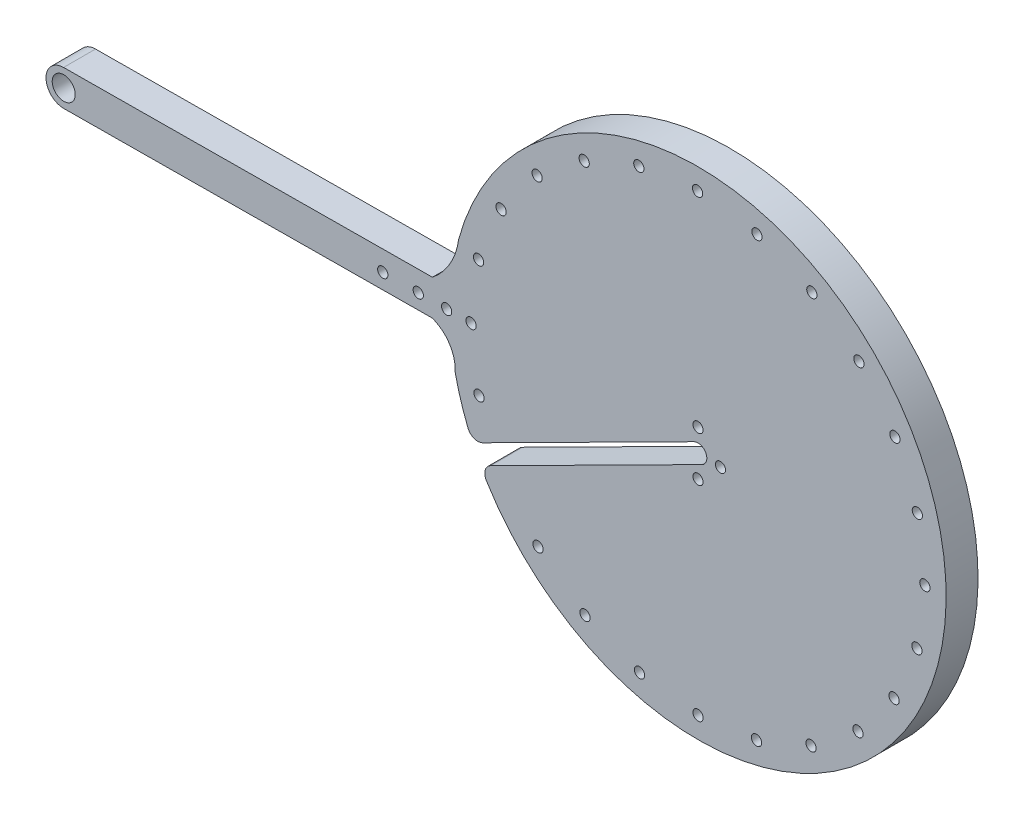
SolidWorks part; units mm, degrees
ref_plane "Front Plane" through (0, 0, 0) normal (0, 0, 1) x (1, 0, 0)
ref_plane "Top Plane" through (0, 0, 0) normal (0, 1, 0) x (1, 0, 0)
ref_plane "Right Plane" through (0, 0, 0) normal (1, 0, 0) x (0, 0, -1)
sketch "Sketch1" plane through (0, 0, 0) normal (0, 0, 1) x (1, 0, 0)
  line L0 (-134.2203, 11.2119) -> (-30.2577, 11.9893)
  line L1 (-30.2577, 21.9896) -> (-30.2577, 11.9893) construction
  line L2 (43.5222, 18.6947) -> (-18.9371, -12.8108)
  line L3 (45.774, 14.2305) -> (-16.6852, -17.275)
  line L5 (-30.2577, 21.9896) -> (-134.2951, 21.2116)
  arc A0 (-23.8494, 2.0369) -> (-30.2577, 11.9893) centre (-33.8306, 2.6493) ccw
  circle A1 centre (44.6612, 22.8126) radius 1.4225
  circle A2 centre (-17.1051, -0.3465) radius 1.45
  arc A3 (-30.2577, 21.9896) -> (-22.8366, 35.0587) centre (-42.6646, 37.6762) ccw
  arc A4 (-134.2951, 21.2116) -> (-134.2203, 11.2119) centre (-134.2577, 16.2117) ccw
  circle A5 centre (-134.2577, 16.2117) radius 3.25
  circle A6 centre (-17.2348, 32.7878) radius 1.45
  circle A7 centre (-10.8866, 48.273) radius 1.45
  circle A8 centre (-19.3514, 16.2033) radius 1.45
  circle A9 centre (-44.2577, 16.208) radius 1.45
  circle A10 centre (-34.2577, 16.2117) radius 1.45
  circle A11 centre (-26.2577, 16.2117) radius 1.45
  circle A12 centre (50.9928, 16.204) radius 1.4225
  circle A13 centre (44.6602, 10.1126) radius 1.4225
  circle A14 centre (106.403, -0.3402) radius 1.45
  circle A15 centre (99.9645, -15.7258) radius 1.45
  circle A16 centre (89.7798, -28.915) radius 1.45
  circle A17 centre (76.5456, -39.0221) radius 1.45
  circle A18 centre (61.1596, -45.3708) radius 1.45
  circle A19 centre (44.6606, -47.5374) radius 1.45
  circle A20 centre (28.16, -45.3771) radius 1.45
  circle A21 centre (12.7695, -39.0329) radius 1.45
  circle A22 centre (-0.471, -28.9276) radius 1.45
  arc A23 (114.5859, 13.512) -> (-22.8366, 35.0587) centre (44.6481, 16.4626) ccw
  arc A24 (-23.8494, 2.0369) -> (-18.9371, -12.8108) centre (44.6481, 16.4626) ccw
  arc A25 (-16.6852, -17.275) -> (114.5859, 13.512) centre (44.6481, 16.4626) ccw
  arc A33 (45.774, 14.2305) -> (43.5222, 18.6947) centre (44.6481, 16.4626) ccw
  circle A34 centre (-0.7303, 61.5936) radius 1.45
  circle A35 centre (12.545, 71.8285) radius 1.45
  circle A36 centre (27.9686, 78.2509) radius 1.45
  circle A37 centre (44.5289, 80.4625) radius 1.45
  circle A38 centre (61.2894, 78.2612) radius 1.45
  circle A39 centre (76.7701, 71.8176) radius 1.45
  circle A40 centre (90.039, 61.5809) radius 1.45
  circle A41 centre (100.2029, 48.2378) radius 1.45
  circle A42 centre (106.5339, 32.7765) radius 1.45
  circle A44 centre (108.6476, 16.2034) radius 1.45
  dimension "D1" = 5
  dimension "D2" = 10
  dimension "D3" = 6.35
  dimension "D4" = 2.845
  dimension "D5" = 2.845
  dimension "D7" = 2.845
  dimension "D9" = 2.9
  dimension "D13" = 70
  dimension "D14" = 64
  dimension "D38" = 20
  dimension "D39" = 10
  dimension "D40" = 10
  dimension "D42" = 5
  dimension "D6" = 6.35
  dimension "D8" = 6.35
  dimension "D10" = 64
  dimension "D11" = 15
  dimension "D12" = 15
  dimension "D15" = 64
  dimension "D16" = 15
  dimension "D17" = 15
  dimension "D18" = 64
  dimension "D19" = 64
  dimension "D20" = 64
  dimension "D21" = 64
  dimension "D22" = 64
  dimension "D23" = 64
  dimension "D24" = 64
  dimension "D25" = 64
  dimension "D26" = 64
  dimension "D27" = 64
  dimension "D28" = 64
  dimension "D29" = 64
  dimension "D30" = 64
  dimension "D31" = 64
  dimension "D32" = 64
  dimension "D33" = 64
  dimension "D34" = 64
  dimension "D35" = 64
  dimension "D36" = 64
  dimension "D37" = 64
  dimension "D41" = 10
  dimension "D43" = 4
  dimension "D44" = 100
extrude "Boss-Extrude2" add sketch "Sketch1" along normal blind 9
fillet "Fillet1" radius 3 1 edges at (-18.9371, -12.8108, 4.5)
fillet "Fillet2" radius 3 1 edges at (-16.6852, -17.275, 4.5)
